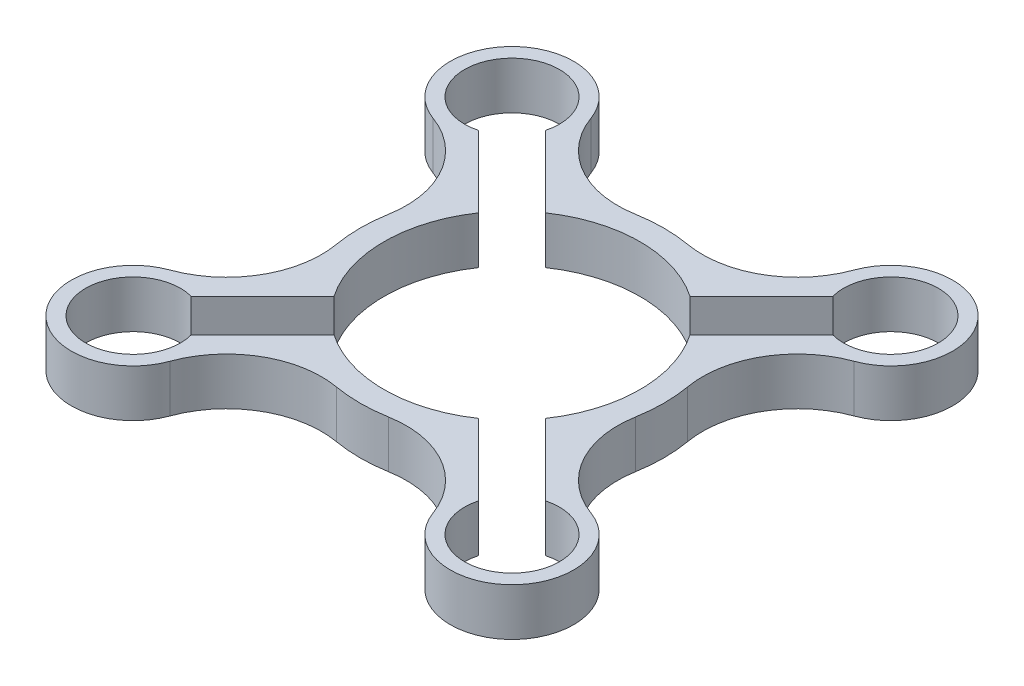
SolidWorks part; units mm, degrees
material "Nickel"
ref_plane "Front Plane" through (0, 0, 0) normal (0, 0, 1) x (1, 0, 0)
ref_plane "Top Plane" through (0, 0, 0) normal (0, 1, 0) x (1, 0, 0)
ref_plane "Right Plane" through (0, 0, 0) normal (1, 0, 0) x (0, 0, -1)
sketch "Sketch1" plane through (0, 0, 0) normal (0, 1, 0) x (1, 0, 0)
  line L0 (-39.9515, 39.9515) -> (0, 0) construction
  line L1 (0, 0) -> (-56.5, 0) construction
  line L2 (-37.3633, 30.2923) -> (-22.2972, 15.2261)
  line L3 (-30.2923, 37.3633) -> (-15.2261, 22.2972)
  line L4 (0, 56.5) -> (0, 0) construction
  line L5 (30.2923, 37.3633) -> (15.2261, 22.2972)
  line L6 (37.3633, 30.2923) -> (22.2972, 15.2261)
  line L7 (37.3633, -30.2923) -> (22.2972, -15.2261)
  line L8 (30.2923, -37.3633) -> (15.2261, -22.2972)
  line L9 (-30.2923, -37.3633) -> (-15.2261, -22.2972)
  line L10 (-37.3633, -30.2923) -> (-22.2972, -15.2261)
  arc A0 (15.2261, 22.2972) -> (-15.2261, 22.2972) centre (0, 0) ccw
  arc A1 (-31.5238, 5.4999) -> (-31.5238, -5.4999) centre (0, 0) ccw
  circle A2 centre (0, 0) radius 56.5 construction
  arc A3 (-30.2923, 37.3633) -> (-37.3633, 30.2923) centre (-39.9515, 39.9515) ccw
  arc A4 (-27.7338, 44.3931) -> (-44.3931, 27.7338) centre (-39.9515, 39.9515) ccw
  arc A5 (-27.7338, 44.3931) -> (-5.4999, 31.5238) centre (-8.9373, 51.2262) ccw
  arc A6 (-44.3931, 27.7338) -> (-31.5238, 5.4999) centre (-51.2262, 8.9373) cw
  arc A7 (44.3931, 27.7338) -> (31.5238, 5.4999) centre (51.2262, 8.9373) ccw
  arc A8 (27.7338, 44.3931) -> (5.4999, 31.5238) centre (8.9373, 51.2262) cw
  arc A9 (27.7338, 44.3931) -> (44.3931, 27.7338) centre (39.9515, 39.9515) cw
  arc A10 (30.2923, 37.3633) -> (37.3633, 30.2923) centre (39.9515, 39.9515) cw
  arc A11 (30.2923, -37.3633) -> (37.3633, -30.2923) centre (39.9515, -39.9515) ccw
  arc A12 (27.7338, -44.3931) -> (44.3931, -27.7338) centre (39.9515, -39.9515) ccw
  arc A13 (27.7338, -44.3931) -> (5.4999, -31.5238) centre (8.9373, -51.2262) ccw
  arc A14 (44.3931, -27.7338) -> (31.5238, -5.4999) centre (51.2262, -8.9373) cw
  arc A15 (-44.3931, -27.7338) -> (-31.5238, -5.4999) centre (-51.2262, -8.9373) ccw
  arc A16 (-27.7338, -44.3931) -> (-5.4999, -31.5238) centre (-8.9373, -51.2262) cw
  arc A17 (-27.7338, -44.3931) -> (-44.3931, -27.7338) centre (-39.9515, -39.9515) cw
  arc A18 (-30.2923, -37.3633) -> (-37.3633, -30.2923) centre (-39.9515, -39.9515) cw
  arc A19 (5.4999, 31.5238) -> (-5.4999, 31.5238) centre (0, 0) ccw
  arc A20 (31.5238, -5.4999) -> (31.5238, 5.4999) centre (0, 0) ccw
  arc A21 (22.2972, -15.2261) -> (22.2972, 15.2261) centre (0, 0) ccw
  arc A22 (-5.4999, -31.5238) -> (5.4999, -31.5238) centre (0, 0) ccw
  arc A23 (-15.2261, -22.2972) -> (15.2261, -22.2972) centre (0, 0) ccw
  arc A24 (-22.2972, 15.2261) -> (-22.2972, -15.2261) centre (0, 0) ccw
  point P6 (0, 56.5)
  dimension "D1" = 64
  dimension "D3" = 54
  dimension "D4" = 20
  dimension "D5" = 26
  dimension "D6" = 113
  dimension "D7" = 20
  dimension "D2" = 45
  dimension "D8" = 10
extrude "Boss-Extrude1" add sketch "Sketch1" along normal blind 10
